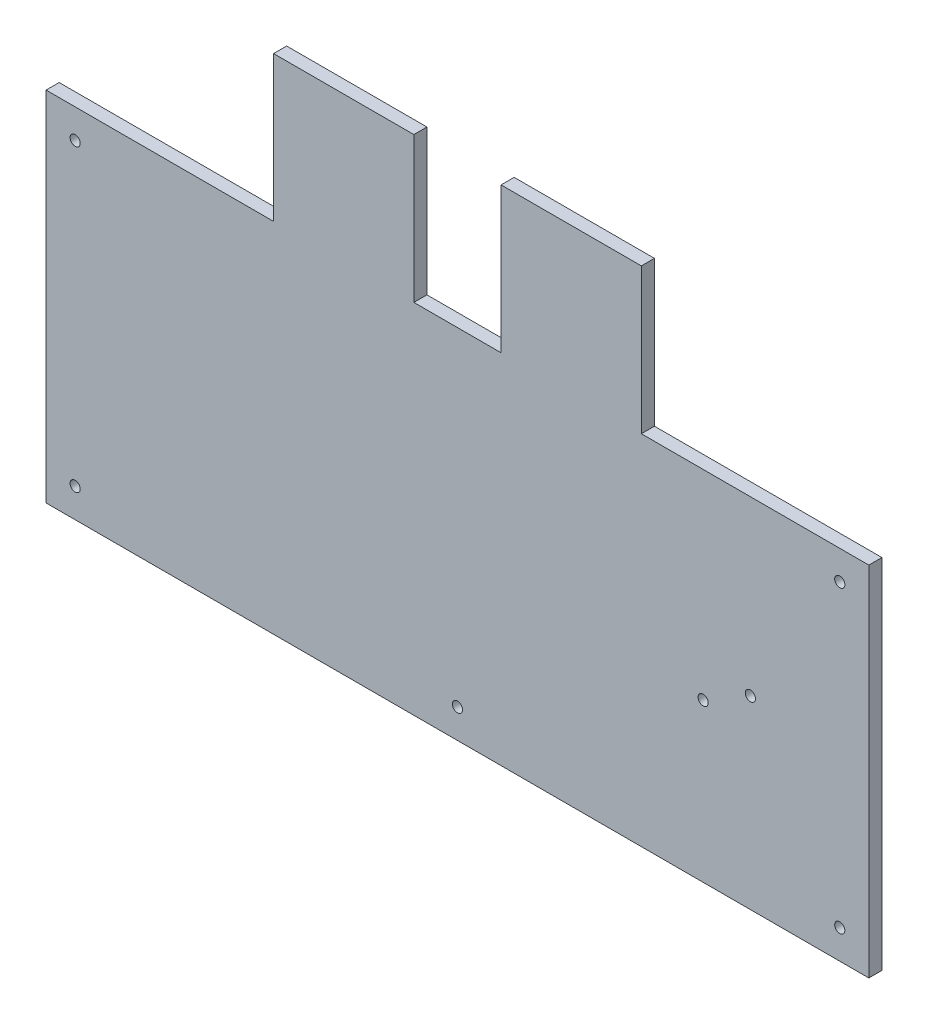
SolidWorks part; units mm, degrees
material "ABS"
ref_plane "Front Plane" through (0, 0, 0) normal (0, 0, 1) x (1, 0, 0)
ref_plane "Top Plane" through (0, 0, 0) normal (0, 1, 0) x (1, 0, 0)
ref_plane "Right Plane" through (0, 0, 0) normal (1, 0, 0) x (0, 0, -1)
sketch "Sketch1" plane through (0, 0, 0) normal (0, 0, 1) x (1, 0, 0)
  line L0 (0, 0) -> (0, 166.746) construction
  line L1 (141.5, -86.5) -> (-141.5, -86.5)
  line L2 (141.5, -86.5) -> (141.5, 86.5)
  line L3 (141.5, 86.5) -> (-141.5, 86.5)
  line L4 (-141.5, -86.5) -> (-141.5, 86.5)
  line L5 (141.5, -86.5) -> (-141.5, 86.5) construction
  line L6 (141.5, 86.5) -> (-141.5, -86.5) construction
  line L7 (0, 0) -> (-259.0657, 0) construction
  circle A0 centre (-131.5, 76.5) radius 1.75
  point P0 (0, 0)
  dimension "D5" = 3.5
  dimension "D1" = 283
  dimension "D2" = 173
  dimension "D3" = 10
  dimension "D4" = 10
extrude "Boss-Extrude1" add sketch "Sketch1" along normal blind 4.5 contours L4 L1 L2 L3 A0 | A0
sketch "Sketch2" plane through (0, 0, 4.5) normal (0, 0, 1) x (1, 0, 0)
  line L0 (0, 0) -> (0, 86.5) construction
  line L1 (141.5, 86.5) -> (-141.5, 86.5) construction
  line L2 (63.25, 86.5) -> (63.25, 36.5)
  line L3 (-141.5, 86.5) -> (-63.25, 86.5)
  line L4 (-141.5, 86.5) -> (-141.5, 36.5)
  line L5 (-141.5, 36.5) -> (-63.25, 36.5)
  line L6 (-63.25, 86.5) -> (-63.25, 36.5)
  line L7 (141.5, 36.5) -> (63.25, 36.5)
  line L8 (141.5, 86.5) -> (141.5, 36.5)
  line L9 (141.5, 86.5) -> (63.25, 86.5)
  line L11 (15, 36.5) -> (-15, 36.5)
  line L12 (15, 36.5) -> (15, 86.5)
  line L13 (15, 86.5) -> (-15, 86.5)
  line L14 (-15, 36.5) -> (-15, 86.5)
  line L15 (15, 36.5) -> (-15, 86.5) construction
  line L16 (15, 86.5) -> (-15, 36.5) construction
  point P14 (0, 61.5)
  dimension "D1" = 50
  dimension "D2" = 126.5
  dimension "D3" = 50
  dimension "D4" = 30
extrude "Cut-Extrude1" cut sketch "Sketch2" against normal up to next
sketch "Sketch3" plane through (0, 0, 4.5) normal (0, 0, 1) x (1, 0, 0)
  line L0 (141.5, -86.5) -> (-141.5, -86.5) construction
  line L2 (-141.5, -86.5) -> (-141.5, 36.5) construction
  line L3 (0, 0) -> (0, -86.5) construction
  line L4 (-141.5, -25) -> (0, -25) construction
  circle A0 centre (-131.5, -76.5) radius 1.75
  circle A1 centre (131.5, -76.5) radius 1.75
  circle A2 centre (131.5, 26.5) radius 1.75
  circle A3 centre (-131.5, 26.5) radius 1.75
  circle A4 centre (0, -76.5) radius 1.75
  dimension "D1" = 3.5
  dimension "D4" = 3.5
  dimension "D2" = 10
  dimension "D3" = 10
  dimension "D5" = 10
extrude "Cut-Extrude2" cut sketch "Sketch3" against normal blind 10
sketch "Sketch5" plane through (0, 0, 4.5) normal (0, 0, 1) x (1, 0, 0)
  line L0 (141.5, -86.5) -> (-141.5, -86.5) construction
  line L1 (141.5, -86.5) -> (141.5, 36.5) construction
  line L2 (100.75, -22.825) -> (84.512, -32.2) construction
  line L3 (84.512, -32.2) -> (108.1011, -32.2) construction
  circle A0 centre (84.512, -32.2) radius 1.75
  circle A1 centre (100.75, -22.825) radius 1.75
  dimension "D4" = 3.5
  dimension "D5" = 3.5
  dimension "D1" = 18.75
  dimension "D2" = 54.3
  dimension "D3" = 40.75
  dimension "D6" = 30
extrude "Cut-Extrude4" cut sketch "Sketch5" against normal up to next
